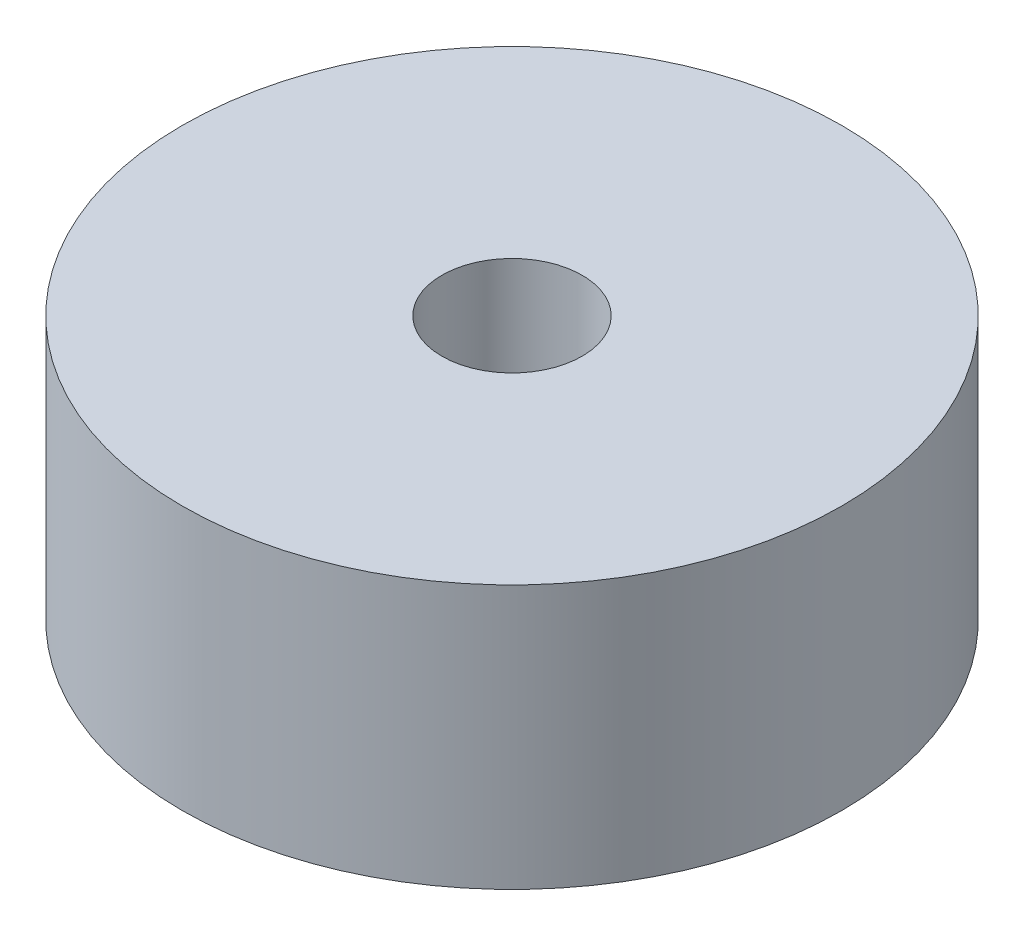
SolidWorks part; units mm, degrees
ref_plane "Front" through (0, 0, 0) normal (0, 0, 1) x (1, 0, 0)
ref_plane "Top" through (0, 0, 0) normal (0, 1, 0) x (1, 0, 0)
ref_plane "Right" through (0, 0, 0) normal (1, 0, 0) x (0, 0, -1)
sketch "Sketch1" plane through (0, 0, 0) normal (0, 1, 0) x (1, 0, 0)
  circle A0 centre (0, 0) radius 7.9375
  circle A1 centre (0, 0) radius 1.6891
  dimension "D1" = 15.875
  dimension "D2" = 3.3782
extrude "Boss-Extrude1" add sketch "Sketch1" along normal blind 6.35
